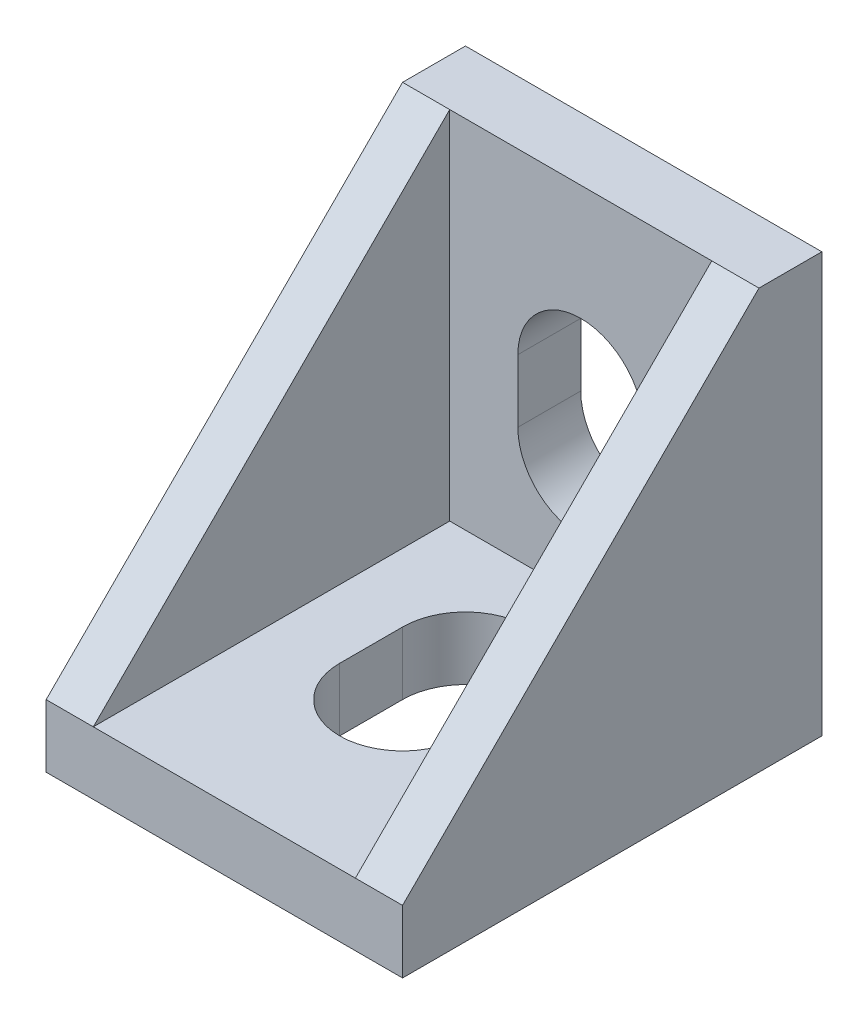
SolidWorks part; units mm, degrees
other "Sunlight"
material "6063-O, Extruded Rod (SS)"
ref_plane "Front Plane" through (0, 0, 0) normal (0, 0, 1) x (1, 0, 0)
ref_plane "Top Plane" through (0, 0, 0) normal (0, 1, 0) x (1, 0, 0)
ref_plane "Right Plane" through (0, 0, 0) normal (1, 0, 0) x (0, 0, -1)
sketch "Sketch4" plane through (0, 0, 0) normal (1, 0, 0) x (0, 0, -1)
  line L0 (7, 10) -> (-10, -7)
  line L1 (7, 10) -> (10, 10)
  line L2 (-10, -7) -> (-10, -10)
  line L3 (-10, -10) -> (10, -10)
  line L4 (10, 10) -> (10, -10)
  line L5 (10, 10) -> (-10, -10) construction
  point P0 (0, 0)
  dimension "D1" = 20
  dimension "D2" = 20
  dimension "D3" = 3
  dimension "D4" = 3
  dimension "D5" = 0
extrude "Boss-Extrude3" add sketch "Sketch4" along normal blind 17
shell "Shell4" thickness 2.25
sketch "Sketch5" plane through (0, 0, -10) normal (0, 0, -1) x (-1, 0, 0)
  line L0 (-11.5, 1.5) -> (-11.5, -1.5)
  line L1 (-5.5, 1.5) -> (-5.5, -1.5)
  line L2 (-8.5, 4.5) -> (-8.5, -4.5) construction
  line L3 (-17, 10) -> (0, 10)
  line L6 (-8.5, 10) -> (-8.5, -10) construction
  line L7 (-17, -10) -> (0, -10) construction
  line L8 (-11.5, 0) -> (-5.5, 0) construction
  line L9 (-17, 0) -> (0, 0) construction
  line L10 (-17, -10) -> (-17, 10) construction
  arc A0 (-5.5, 1.5) -> (-11.5, 1.5) centre (-8.5, 1.5) ccw
  arc A1 (-11.5, -1.5) -> (-5.5, -1.5) centre (-8.5, -1.5) ccw
  point P3 (-8.5, 4.5)
  point P8 (-8.5, -4.5)
  point P19 (-17, 10)
  point P21 (-8.5, 10)
  dimension "D1" = 6
  dimension "D2" = 9
  dimension "D3" = 0
  dimension "D4" = 0
extrude "Cut-Extrude1" cut sketch "Sketch5" against normal through all contours L1 A1 L0 A0
sketch "Sketch8" plane through (0, -10, 0) normal (0, -1, 0) x (-1, 0, 0)
  line L0 (-11.5, 1.5) -> (-11.5, -1.5)
  line L1 (-5.5, 1.5) -> (-5.5, -1.5)
  line L2 (-8.5, 4.5) -> (-8.5, -4.5) construction
  line L3 (-8.5, 10) -> (-8.5, -10) construction
  line L4 (-17, 10) -> (0, 10) construction
  line L5 (-17, -10) -> (0, -10) construction
  line L6 (-17, 0) -> (0, 0) construction
  line L8 (-11.5, 0) -> (-5.5, 0) construction
  line L9 (-17, -10) -> (-17, 10) construction
  line L11 (0, -10) -> (0, 10) construction
  arc A0 (-5.5, 1.5) -> (-11.5, 1.5) centre (-8.5, 1.5) ccw
  arc A1 (-11.5, -1.5) -> (-5.5, -1.5) centre (-8.5, -1.5) ccw
  point P3 (-8.5, 4.5)
  point P8 (-8.5, -4.5)
  dimension "D1" = 6
  dimension "D2" = 9
  dimension "D3" = 0
  dimension "D4" = 0
extrude "Cut-Extrude2" cut sketch "Sketch8" against normal through all
sketch "Sketch9" plane through (0, 0, -10) normal (0, 0, -1) x (-1, 0, 0)
  line L0 (-9.525, 8.125) -> (-7.475, 8.125)
  line L1 (-9.525, 6.375) -> (-7.475, 6.375)
  line L2 (-8.5, 10) -> (-8.5, -10) construction
  line L3 (-17, 10) -> (0, 10) construction
  line L4 (-17, -10) -> (0, -10) construction
  line L5 (-8.5, 8.125) -> (-8.5, 6.375) construction
  line L6 (-17, 4.5) -> (0, 4.5) construction
  line L7 (-8.5, 4.5) -> (0, 4.5) construction
  line L9 (0, 10) -> (0, 4.5) construction
  line L10 (0, -10) -> (0, 10) construction
  line L11 (0, 7.25) -> (-17, 7.25) construction
  line L12 (-17, -10) -> (-17, 10) construction
  line L13 (-10.4, 7.25) -> (-6.6, 7.25) construction
  arc A0 (-7.475, 6.375) -> (-7.475, 8.125) centre (-7.475, 7.25) ccw
  arc A1 (-9.525, 8.125) -> (-9.525, 6.375) centre (-9.525, 7.25) ccw
  arc A2 (-5.5, 1.5) -> (-11.5, 1.5) centre (-8.5, 1.5) ccw construction
  point P1 (-10.4, 7.25)
  point P3 (-6.6, 7.25)
  point P24 (-8.5, 4.5)
  point P25 (-8.5, 4.5)
  dimension "D1" = 1.75
  dimension "D2" = 3.8
  dimension "D3" = 0
  dimension "D4" = 0
  dimension "D5" = 0
  dimension "D6" = 0
extrude "Boss-Extrude4" add sketch "Sketch9" along normal blind 1
sketch "Sketch10" plane through (0, 0, -10) normal (0, 0, -1) x (-1, 0, 0)
  line L0 (-9.525, -6.375) -> (-7.475, -6.375)
  line L1 (-9.525, -8.125) -> (-7.475, -8.125)
  line L2 (-8.5, 10) -> (-8.5, -10) construction
  line L5 (-8.5, -6.375) -> (-8.5, -8.125) construction
  line L6 (-17, 10) -> (0, 10) construction
  line L7 (-17, -10) -> (0, -10) construction
  line L8 (-8.5, -4.5) -> (0, -4.5) construction
  line L11 (0, -10) -> (0, 10) construction
  line L13 (-10.4, -7.25) -> (-6.6, -7.25) construction
  line L14 (0, -4.5) -> (0, -10) construction
  line L15 (0, -7.25) -> (-17, -7.25) construction
  line L16 (-17, -10) -> (-17, 10) construction
  arc A0 (-7.475, -8.125) -> (-7.475, -6.375) centre (-7.475, -7.25) ccw
  arc A1 (-9.525, -6.375) -> (-9.525, -8.125) centre (-9.525, -7.25) ccw
  arc A3 (-11.5, -1.5) -> (-5.5, -1.5) centre (-8.5, -1.5) ccw construction
  point P1 (-10.4, -7.25)
  point P3 (-6.6, -7.25)
  point P24 (-8.3945, -3.5679)
  point P25 (-8.3945, -3.5679)
  dimension "D1" = 1.75
  dimension "D2" = 3.8
  dimension "D3" = 0
  dimension "D4" = 0
extrude "Boss-Extrude5" add sketch "Sketch10" along normal blind 1
sketch "Sketch12" plane through (-0.8438, -10, -7.7593) normal (0, -1, 0) x (-1, 0, 0)
  line L0 (-10.3688, 0.3657) -> (-8.3188, 0.3657)
  line L1 (-10.3688, -1.3843) -> (-8.3188, -1.3843)
  line L2 (-9.3438, 10) -> (-9.3438, -10) construction
  line L5 (-9.3438, 0.3657) -> (-9.3438, -1.3843) construction
  line L6 (-9.3438, -3.2593) -> (-0.8438, -3.2593) construction
  line L7 (-0.8438, -17.7593) -> (-0.8438, 2.2407) construction
  line L8 (-0.8438, -3.2593) -> (-0.8438, 2.2407) construction
  line L9 (-0.8438, -0.5093) -> (-17.8438, -0.5093) construction
  line L11 (-17.8438, -17.7593) -> (-17.8438, 2.2407) construction
  line L13 (-11.2438, -0.5093) -> (-7.4438, -0.5093) construction
  line L14 (-9.3438, 2.2407) -> (-9.3438, -3.2593) construction
  line L15 (-10.3688, 2.2407) -> (-8.3188, 2.2407) construction
  arc A0 (-8.3188, -1.3843) -> (-8.3188, 0.3657) centre (-8.3188, -0.5093) ccw
  arc A1 (-10.3688, 0.3657) -> (-10.3688, -1.3843) centre (-10.3688, -0.5093) ccw
  arc A3 (-6.3438, -6.2593) -> (-12.3438, -6.2593) centre (-9.3438, -6.2593) ccw construction
  point P1 (-11.2438, -0.5093)
  point P3 (-7.4438, -0.5093)
  point P24 (-8.5, 4.5)
  point P25 (-8.5, 4.5)
  dimension "D1" = 1.75
  dimension "D2" = 3.8
  dimension "D3" = 0
  dimension "D4" = 0
  dimension "D5" = 0
extrude "Boss-Extrude6" add sketch "Sketch12" along normal blind 1
sketch "Sketch14" plane through (-0.8438, -10, -7.7593) normal (0, -1, 0) x (-1, 0, 0)
  line L0 (-10.3688, -14.1343) -> (-8.3188, -14.1343)
  line L1 (-10.3688, -15.8843) -> (-8.3188, -15.8843)
  line L2 (-9.3438, 2.2407) -> (-9.3438, -17.7593) construction
  line L3 (-10.3688, 2.2407) -> (-8.3188, 2.2407) construction
  line L4 (-17.8438, -17.7593) -> (-0.8438, -17.7593) construction
  line L5 (-9.3438, -14.1343) -> (-9.3438, -15.8843) construction
  line L8 (-9.3438, -12.2593) -> (-0.8438, -12.2593) construction
  line L9 (-0.8438, -17.7593) -> (-0.8438, 2.2407) construction
  line L10 (-0.8438, -12.2593) -> (-0.8438, -17.7593) construction
  line L12 (-0.8438, -15.0093) -> (-17.8438, -15.0093) construction
  line L13 (-11.2438, -15.0093) -> (-7.4438, -15.0093) construction
  line L14 (-17.8438, -17.7593) -> (-17.8438, 2.2407) construction
  arc A0 (-8.3188, -15.8843) -> (-8.3188, -14.1343) centre (-8.3188, -15.0093) ccw
  arc A1 (-10.3688, -14.1343) -> (-10.3688, -15.8843) centre (-10.3688, -15.0093) ccw
  arc A2 (-12.3438, -9.2593) -> (-6.3438, -9.2593) centre (-9.3438, -9.2593) ccw construction
  point P1 (-11.2438, -15.0093)
  point P3 (-7.4438, -15.0093)
  point P24 (-8.3945, -3.5679)
  point P25 (-8.3945, -3.5679)
  dimension "D1" = 1.75
  dimension "D2" = 3.8
  dimension "D3" = 0
  dimension "D4" = 0
extrude "Boss-Extrude7" add sketch "Sketch14" along normal blind 1
